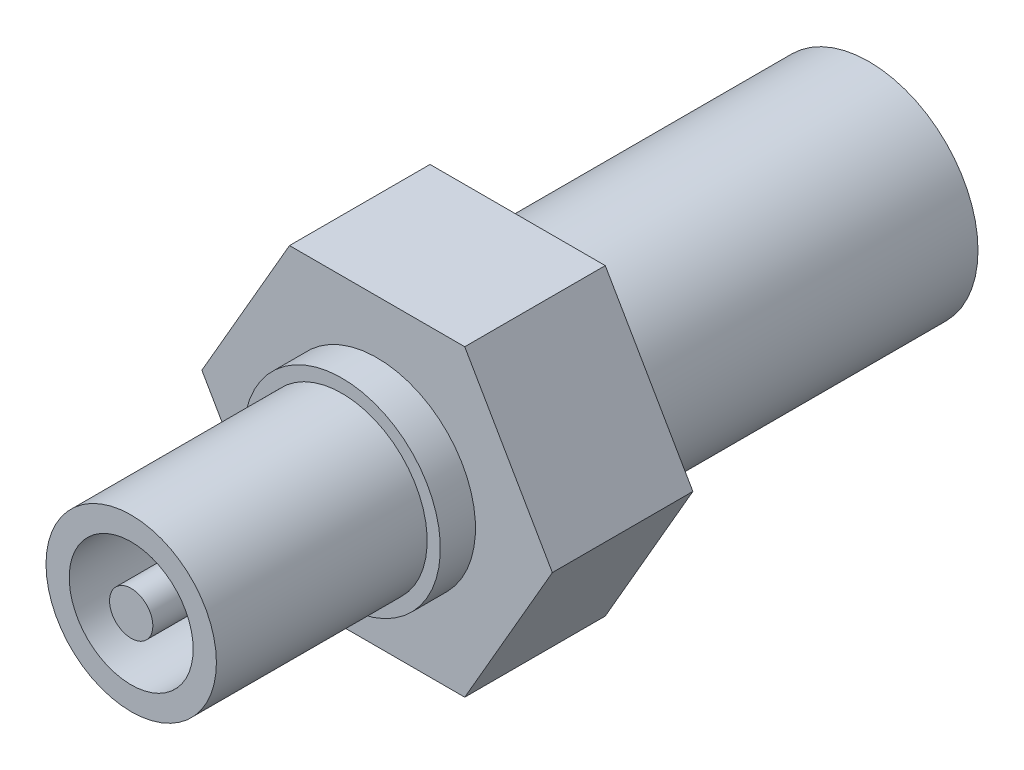
SolidWorks part; units mm, degrees
material "Chrome Stainless Steel"
ref_plane "Front Plane" through (0, 0, 0) normal (0, 0, 1) x (1, 0, 0)
ref_plane "Top Plane" through (0, 0, 0) normal (0, 1, 0) x (1, 0, 0)
ref_plane "Right Plane" through (0, 0, 0) normal (1, 0, 0) x (0, 0, -1)
sketch "Sketch1" plane through (0, 0, 0) normal (0, 0, 1) x (1, 0, 0)
  circle A0 centre (0, 0) radius 3.85
extrude "Extrude1" add sketch "Sketch1" along normal blind 9.525
sketch "Sketch2" plane through (0, 0, 0) normal (0, 0, -1) x (-1, 0, 0)
  circle A0 centre (0, 0) radius 4.445
extrude "Extrude2" add sketch "Sketch2" along normal blind 1.5875
sketch "Sketch3" plane through (0, 0, -1.5875) normal (0, 0, -1) x (-1, 0, 0)
  line L0 (-3.9595, 6.858) -> (3.9595, 6.858)
  line L1 (3.9595, 6.858) -> (7.9189, 0)
  line L2 (7.9189, 0) -> (3.9595, -6.858)
  line L3 (3.9595, -6.858) -> (-3.9595, -6.858)
  line L4 (-3.9595, -6.858) -> (-7.9189, 0)
  line L5 (-7.9189, 0) -> (-3.9595, 6.858)
  line L6 (0, 0) -> (-3.9595, 6.858) construction
  line L7 (0, 0) -> (3.9595, 6.858) construction
  dimension "D1" = 13.716
extrude "Extrude3" add sketch "Sketch3" along normal blind 6.35
sketch "Sketch4" plane through (0, 0, -7.9375) normal (0, 0, -1) x (-1, 0, 0)
  circle A0 centre (0, 0) radius 4.9276
extrude "Extrude4" add sketch "Sketch4" along normal blind 15.875
sketch "Sketch5" plane through (0, 0, 9.525) normal (0, 0, 1) x (1, 0, 0)
  circle A0 centre (0, 0) radius 2.8004
  circle A1 centre (0, 0) radius 0.9779
extrude "Cut-Extrude1" cut sketch "Sketch5" against normal blind 9.525
